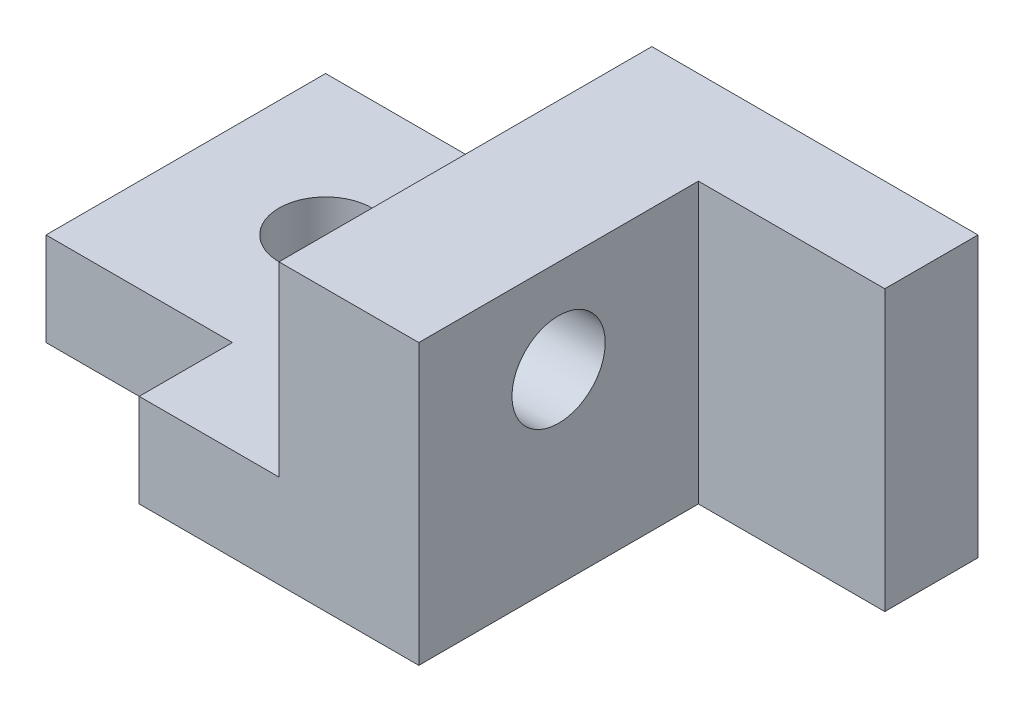
SolidWorks part; units mm, degrees
ref_plane "Front Plane" through (0, 0, 0) normal (0, 0, 1) x (1, 0, 0)
ref_plane "Top Plane" through (0, 0, 0) normal (0, 1, 0) x (1, 0, 0)
ref_plane "Right Plane" through (0, 0, 0) normal (1, 0, 0) x (0, 0, -1)
sketch "Sketch1" plane through (0, 0, 0) normal (0, 1, 0) x (1, 0, 0)
  line L1 (0, 0) -> (70, 0)
  line L2 (0, 0) -> (0, 40)
  line L3 (0, 40) -> (70, 40)
  line L4 (70, 0) -> (70, 40)
  dimension "D1" = 70
  dimension "D2" = 40
extrude "Boss-Extrude1" add sketch "Sketch1" along normal blind 30
sketch "Sketch3" plane through (0, 30, 0) normal (0, 1, 0) x (1, 0, 0)
  line L0 (70, 40) -> (70, 30) construction
  line L1 (70, 0) -> (70, 40) construction
  line L2 (0, 0) -> (70, 0) construction
  line L3 (70, 30) -> (50, 30)
  line L4 (70, 30) -> (70, 0)
  line L5 (70, 0) -> (50, 0)
  line L6 (50, 30) -> (50, 0)
  dimension "D1" = 10
  dimension "D2" = 20
extrude "Cut-Extrude1" cut sketch "Sketch3" against normal through all and the other way through all
sketch "Sketch4" plane through (0, 0, 0) normal (0, 0, 1) x (1, 0, 0)
  line L0 (50, 30) -> (35, 30) construction
  line L1 (0, 30) -> (50, 30) construction
  line L2 (0, 30) -> (0, 0) construction
  line L3 (35, 30) -> (0, 30)
  line L4 (35, 30) -> (35, 10)
  line L5 (35, 10) -> (0, 10)
  line L6 (0, 30) -> (0, 10)
  dimension "D1" = 15
  dimension "D2" = 20
extrude "Cut-Extrude2" cut sketch "Sketch4" against normal through all contours L4 L3 L6 L5
sketch "Sketch5" plane through (50, 0, 0) normal (1, 0, 0) x (0, 0, -1)
  line L0 (0, 30) -> (15, 30) construction
  line L1 (0, 30) -> (30, 30) construction
  line L2 (15, 30) -> (15, 20) construction
  circle A0 centre (15, 20) radius 5
  dimension "D2" = 10
  dimension "D1" = 10
extrude "Cut-Extrude3" cut sketch "Sketch5" against normal blind 30 contours A0
sketch "Sketch6" plane through (0, 10, 0) normal (0, 1, 0) x (1, 0, 0)
  line L1 (0, 0) -> (20, 0)
  line L2 (0, 0) -> (0, 10)
  line L3 (0, 10) -> (20, 10)
  line L4 (20, 0) -> (20, 10)
  dimension "D1" = 10
  dimension "D2" = 20
extrude "Cut-Extrude4" cut sketch "Sketch6" against normal through all
sketch "Sketch7" plane through (0, 10, 0) normal (0, 1, 0) x (1, 0, 0)
  line L0 (0, 10) -> (0, 25) construction
  line L1 (0, 40) -> (0, 10) construction
  line L2 (0, 25) -> (15, 25) construction
  circle A0 centre (15, 25) radius 5
  dimension "D2" = 10
  dimension "D1" = 15
extrude "Cut-Extrude5" cut sketch "Sketch7" against normal blind 30 contours A0
